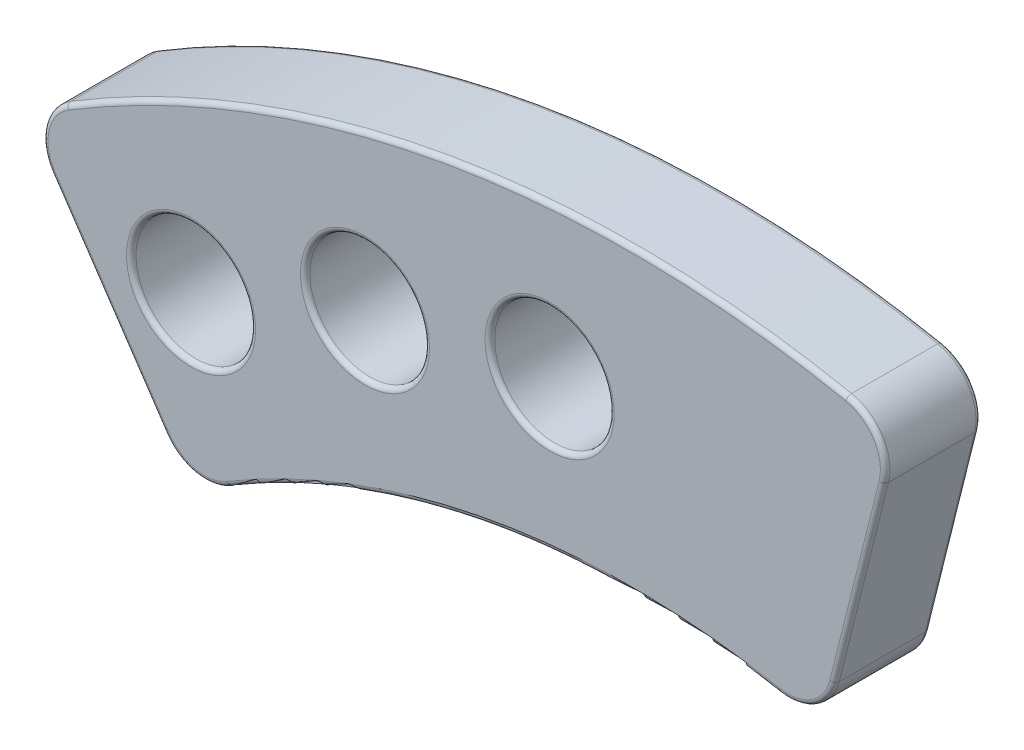
SolidWorks part; units mm, degrees
ref_plane "Piano frontale" through (0, 0, 0) normal (0, 0, 1) x (1, 0, 0)
ref_plane "Piano superiore" through (0, 0, 0) normal (0, 1, 0) x (1, 0, 0)
ref_plane "Piano destro" through (0, 0, 0) normal (1, 0, 0) x (0, 0, -1)
sketch "Schizzo1" plane through (0, 0, 0) normal (0, 0, 1) x (1, 0, 0)
  line L0 (0, 0) -> (0.0019, 0.0173)
  line L1 (11.033, 44.1375) -> (8.0008, 32.0099)
  line L2 (-25.4287, 37.7256) -> (-18.4416, 27.3597)
  line L3 (0.0019, 0.0173) -> (-0.0017, 0.0026)
  arc A0 (8.0008, 32.0099) -> (-18.4416, 27.3597) centre (0, 0) ccw
  arc A1 (11.033, 44.1375) -> (-25.4287, 37.7256) centre (0, 0) ccw
  circle A3 centre (-18.4416, 34.6422) radius 2.5
  circle A5 centre (-11.1648, 37.6234) radius 2.5
  circle A6 centre (-3.4398, 39.094) radius 2.5
  point P18 (0, 0)
  dimension "D1" = 3
extrude "Estrusione-Estrusione1" add sketch "Schizzo1" along normal blind 4 contours L1 A1 L2 A0 A6 A5 A3
fillet "Raccordo1" radius 2 4 edges at (-18.4416, 27.3597, 2) (8.0008, 32.0099, 2) (11.033, 44.1375, 2) (-25.4287, 37.7256, 2)
fillet "Raccordo2" radius 0.2 22 edges at (-24.5805, 37.5742, 4) (-7.8796, 44.808, 4) (10.2873, 43.7057, 4) (9.5044, 38.0235, 4) (7.6094, 32.6948, 4) (-5.7147, 32.496, 4) (-18.3073, 28.1371, 4) (-21.9063, 32.4999, 4) (-15.9416, 34.6422, 4) (-8.6648, 37.6234, 4) (-0.9398, 39.094, 4) (7.6094, 32.6948, 0) (9.5044, 38.0235, 0) (10.2873, 43.7057, 0) (-7.8796, 44.808, 0) (-24.5805, 37.5742, 0) (-21.9063, 32.4999, 0) (-18.3073, 28.1371, 0) (-5.7147, 32.496, 0) (-15.9416, 34.6422, 0) (-8.6648, 37.6234, 0) (-0.9398, 39.094, 0)
